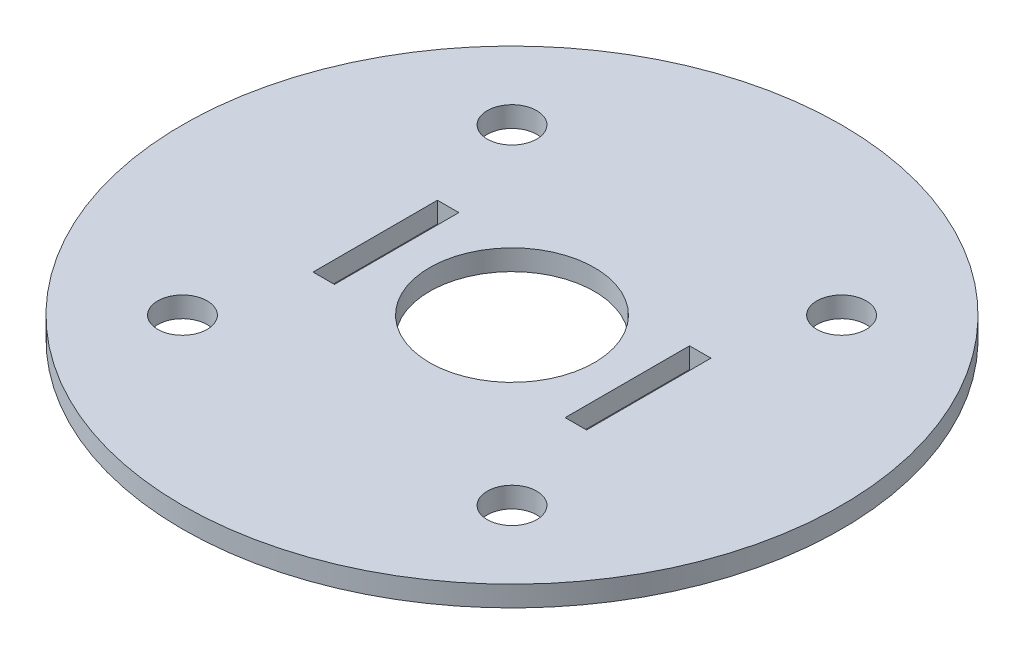
SolidWorks part; units mm, degrees
ref_plane "Front Plane" through (0, 0, 0) normal (0, 0, 1) x (1, 0, 0)
ref_plane "Top Plane" through (0, 0, 0) normal (0, 1, 0) x (1, 0, 0)
ref_plane "Right Plane" through (0, 0, 0) normal (1, 0, 0) x (0, 0, -1)
sketch "Sketch1" plane through (0, 0, 0) normal (0, 1, 0) x (1, 0, 0)
  line L0 (0, 0) -> (-33.3085, 0) construction
  line L1 (0, 0) -> (0, 25.0094) construction
  line L2 (21.082, -9.5885) -> (17.78, -9.5885)
  line L3 (-21.082, 9.5885) -> (-17.78, 9.5885)
  line L4 (-21.082, 9.5885) -> (-21.082, -9.5885)
  line L5 (-21.082, -9.5885) -> (-17.78, -9.5885)
  line L6 (-17.78, 9.5885) -> (-17.78, -9.5885)
  line L7 (21.082, 9.5885) -> (21.082, -9.5885)
  line L8 (21.082, 9.5885) -> (17.78, 9.5885)
  line L9 (17.78, 9.5885) -> (17.78, -9.5885)
  line L11 (0, 35.1953) -> (-30.48, 17.5976) construction
  line L12 (-30.48, 17.5976) -> (-30.48, -17.5976) construction
  line L13 (-30.48, -17.5976) -> (0, -35.1953) construction
  line L14 (0, -35.1953) -> (30.48, -17.5976) construction
  line L15 (30.48, -17.5976) -> (30.48, 17.5976) construction
  line L16 (30.48, 17.5976) -> (0, 35.1953) construction
  circle A0 centre (0, 0) radius 50.8
  circle A1 centre (-25.4, 25.4) radius 3.81
  circle A2 centre (-25.4, -25.4) radius 3.81
  circle A3 centre (25.4, -25.4) radius 3.81
  circle A4 centre (25.4, 25.4) radius 3.81
  circle A5 centre (0, 0) radius 30.48 construction
  circle A6 centre (0, 0) radius 12.7
  dimension "D1" = 101.6
  dimension "D2" = 7.62
  dimension "D9" = 60.96
  dimension "D11" = 25.4
  dimension "D3" = 25.4
  dimension "D4" = 25.4
  dimension "D5" = 3.302
  dimension "D6" = 19.177
  dimension "D7" = 17.78
  dimension "D8" = 9.5885
  dimension "D10" = 35.1953
extrude "Boss-Extrude1" add sketch "Sketch1" along normal blind 3.175
